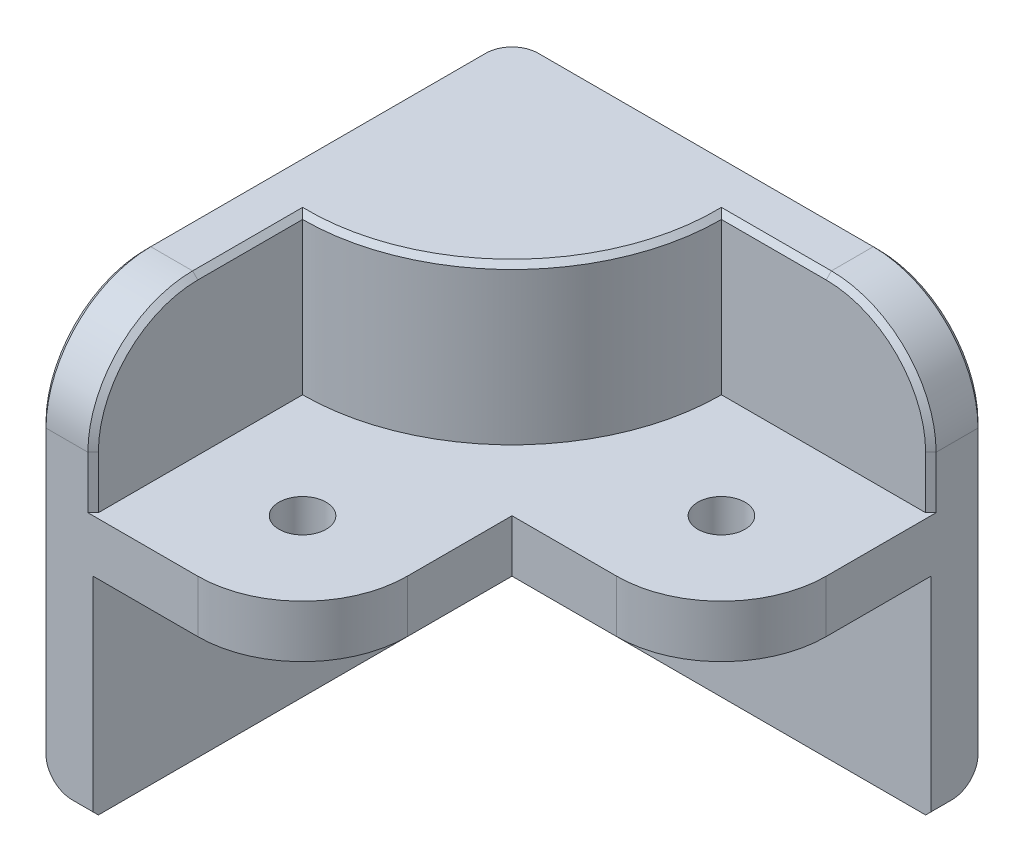
SolidWorks part; units mm, degrees
ref_plane "Front Plane" through (0, 0, 0) normal (0, 0, 1) x (1, 0, 0)
ref_plane "Top Plane" through (0, 0, 0) normal (0, 1, 0) x (1, 0, 0)
ref_plane "Right Plane" through (0, 0, 0) normal (1, 0, 0) x (0, 0, -1)
sketch "Sketch1" plane through (0, 0, 0) normal (0, 1, 0) x (1, 0, 0)
  line L0 (0, 0) -> (0, -45)
  line L1 (0, -45) -> (5, -45)
  line L2 (5, -45) -> (5, -5)
  line L3 (5, -5) -> (45, -5)
  line L4 (45, -5) -> (45, 0)
  line L5 (45, 0) -> (0, 0)
  dimension "D1" = 5
  dimension "D2" = 40
extrude "Boss-Extrude1" add sketch "Sketch1" against normal blind 40
sketch "Sketch2" plane through (0, -40, 0) normal (0, -1, 0) x (1, 0, 0)
  line L0 (5, 45) -> (25, 45)
  line L1 (25, 45) -> (25, 25)
  line L2 (25, 25) -> (45, 25)
  line L3 (45, 25) -> (45, 5)
  line L4 (45, 5) -> (5, 5)
  line L5 (5, 5) -> (5, 45)
  dimension "D1" = 20
extrude "Boss-Extrude2" add sketch "Sketch2" against normal blind 5 from offset 20 offset against normal yes
fillet "Fillet1" radius 10 4 edges at (45, 0, 2.5) (2.5, 0, 45) (25, -17.5, 45) (45, -17.5, 25)
fillet "Fillet2" radius 3 3 edges at (0, -40, 22.5) (0, -20, 0) (22.5, -40, 0)
hole_wizard "M4 Clearance Hole1" positions "Sketch3" profile "Sketch4" hole size "M4" standard "ANSI Metric" end condition through all
sketch "Sketch3" plane through (0, -15, 0) normal (0, 1, 0) x (1, 0, 0)
  arc A0 (15, -45) -> (25, -35) centre (15, -35) ccw construction
  arc A1 (35, -25) -> (45, -15) centre (35, -15) ccw construction
  point P0 (35, -15)
  point P2 (15, -35)
  point P8 (0, 0)
  point P9 (0, 0)
sketch "Sketch4" plane through (35, -15, 15) normal (1, 0, 0) x (0, 0, 1)
  line L0 (0, 0) -> (0, 25)
  line L1 (0, 25) -> (2.25, 25)
  line L2 (2.25, 25) -> (2.25, 0)
  line L5 (2.25, 0) -> (0, 0)
  line L11 (0, -6.35) -> (0, 107.95) construction
  dimension "Thru Hole Dia." = 4.5
  dimension "Thru Hole Depth" = 25
sketch "Sketch5" plane through (0, 0, 0) normal (0, 1, 0) x (1, 0, 0)
  line L0 (5, -5) -> (35, -5) construction
  line L1 (5, -35) -> (5, -5) construction
  line L2 (5, -25) -> (5, -5)
  line L3 (5, -5) -> (25, -5)
  arc A0 (25, -5) -> (5, -25) centre (5, -5) cw
  dimension "D1" = 20
extrude "Boss-Extrude3" add sketch "Sketch5" against normal up to next
chamfer "Chamfer1" distance 0.5 angle 45 18 edges at (4, -40, 45) (45, -40, 4) (0.8787, -39.1213, 45) (45, -39.1213, 0.8787) (0, -23.5, 45) (45, -23.5, 0) (0, -2.9289, 42.0711) (42.0711, -2.9289, 0) (0, 0, 19) (0.8787, 0, 0.8787) (19, 0, 0) (5, -12.5, 45) (45, -12.5, 5) (5, -2.9289, 42.0711) (42.0711, -2.9289, 5) (5, 0, 30) (30, 0, 5) (19.1421, 0, 19.1421)
